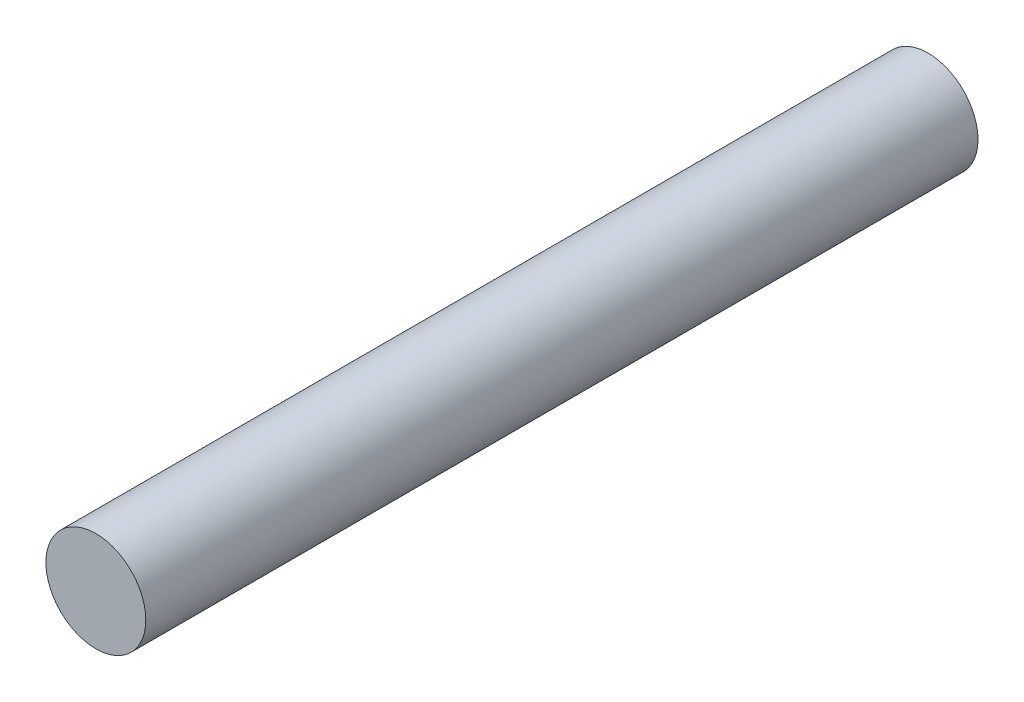
SolidWorks part; units mm, degrees
ref_plane "前视基准面" through (0, 0, 0) normal (0, 0, 1) x (1, 0, 0)
ref_plane "上视基准面" through (0, 0, 0) normal (0, 1, 0) x (1, 0, 0)
ref_plane "右视基准面" through (0, 0, 0) normal (1, 0, 0) x (0, 0, -1)
other "Configuration Table"
sketch "草图1" plane through (0, 0, 0) normal (0, 0, 1) x (1, 0, 0)
  circle A0 centre (0, 0) radius 1.5
extrude "凸台-拉伸1" add sketch "草图1" along normal blind 25
